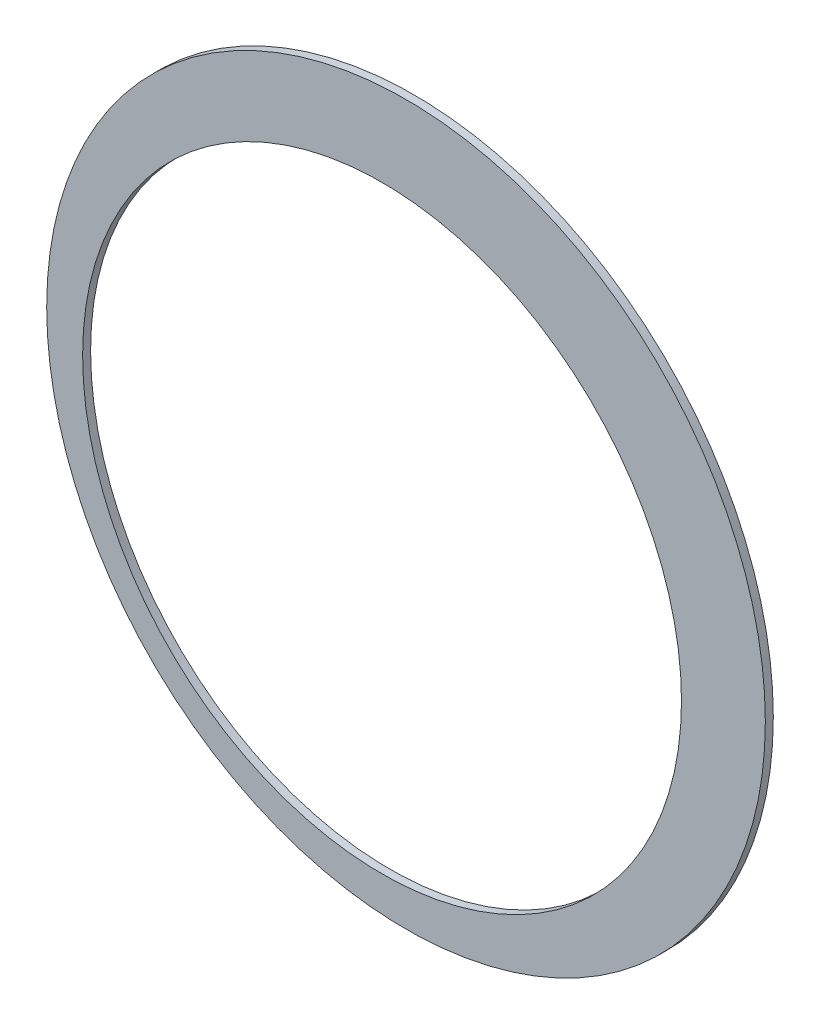
SolidWorks part; units mm, degrees
ref_plane "Front" through (0, 0, 0) normal (0, 0, 1) x (1, 0, 0)
ref_plane "Top" through (0, 0, 0) normal (0, 1, 0) x (1, 0, 0)
ref_plane "Right" through (0, 0, 0) normal (1, 0, 0) x (0, 0, -1)
sketch "Sketch1" plane through (0, 0, 0) normal (0, 0, 1) x (1, 0, 0)
  circle A0 centre (0, 0) radius 37.5
  circle A1 centre (3, 3) radius 45
  point P3 (3, 3)
  dimension "D1" = 75
  dimension "D4" = 90
  dimension "D2" = 3
  dimension "D3" = 3
sketch "Sketch2" plane through (0, 0, 0) normal (0, 0, 1) x (1, 0, 0)
  circle A0 centre (3, 3) radius 45
extrude "Base-Extrude" add sketch "Sketch2" along normal blind 1
sketch "Sketch3" plane through (0, 0, 0) normal (0, 0, 1) x (1, 0, 0)
  circle A0 centre (0, 0) radius 37.5
extrude "Cut-Extrude5" cut sketch "Sketch3" along normal through all
